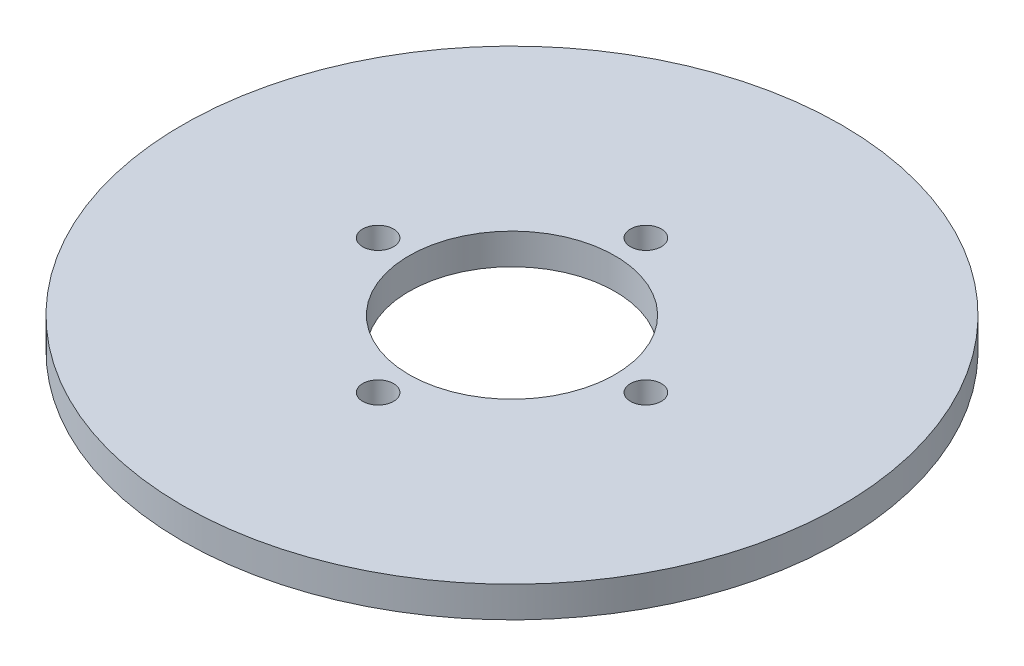
SolidWorks part; units mm, degrees
material "6063-O"
ref_plane "Front Plane" through (0, 0, 0) normal (0, 0, 1) x (1, 0, 0)
ref_plane "Top Plane" through (0, 0, 0) normal (0, 1, 0) x (1, 0, 0)
ref_plane "Right Plane" through (0, 0, 0) normal (1, 0, 0) x (0, 0, -1)
sketch "Sketch1" plane through (0, 0, 0) normal (0, 1, 0) x (1, 0, 0)
  circle A0 centre (0, 0) radius 32
  dimension "D1" = 64
extrude "Boss-Extrude1" add sketch "Sketch1" along normal blind 3
sketch "Sketch2" plane through (0, 3, 0) normal (0, 1, 0) x (1, 0, 0)
  circle A0 centre (0, 0) radius 10
  dimension "D1" = 20
extrude "Cut-Extrude1" cut sketch "Sketch2" against normal blind 10
sketch "Sketch3" plane through (0, 0, 0) normal (0, -1, 0) x (1, 0, 0)
  arc A0 (-1.4975, 12.9135) -> (-12.9135, 1.4975) centre (0, 0) ccw construction
  circle A1 centre (0, 13) radius 1.5
  arc A2 (-1.4975, 12.9135) -> (-12.9135, 1.4975) centre (0, 0) ccw
  circle A3 centre (13, 0) radius 1.5
  arc A4 (-1.4975, 12.9135) -> (-12.9135, 1.4975) centre (0, 0) ccw
  circle A5 centre (0, -13) radius 1.5
  arc A6 (-1.4975, 12.9135) -> (-12.9135, 1.4975) centre (0, 0) ccw
  circle A7 centre (-13, 0) radius 1.5
  arc A8 (12.9135, 1.4975) -> (1.4975, 12.9135) centre (0, 0) ccw construction
  arc A9 (12.9135, 1.4975) -> (1.4975, 12.9135) centre (0, 0) ccw
  arc A10 (12.9135, 1.4975) -> (1.4975, 12.9135) centre (0, 0) ccw
  arc A11 (12.9135, 1.4975) -> (1.4975, 12.9135) centre (0, 0) ccw
  arc A12 (1.4975, -12.9135) -> (12.9135, -1.4975) centre (0, 0) ccw construction
  arc A13 (1.4975, -12.9135) -> (12.9135, -1.4975) centre (0, 0) ccw
  arc A14 (1.4975, -12.9135) -> (12.9135, -1.4975) centre (0, 0) ccw
  arc A15 (1.4975, -12.9135) -> (12.9135, -1.4975) centre (0, 0) ccw
  arc A16 (-12.9135, -1.4975) -> (-1.4975, -12.9135) centre (0, 0) ccw construction
  arc A17 (-12.9135, -1.4975) -> (-1.4975, -12.9135) centre (0, 0) ccw
  arc A18 (-12.9135, -1.4975) -> (-1.4975, -12.9135) centre (0, 0) ccw
  arc A19 (-12.9135, -1.4975) -> (-1.4975, -12.9135) centre (0, 0) ccw
  point P17 (0, 0)
  dimension "D1" = 26
  dimension "D2" = 3
  dimension "D3" = 4
extrude "Cut-Extrude2" cut sketch "Sketch3" against normal through all contours A3 | A5 | A7 | A1
